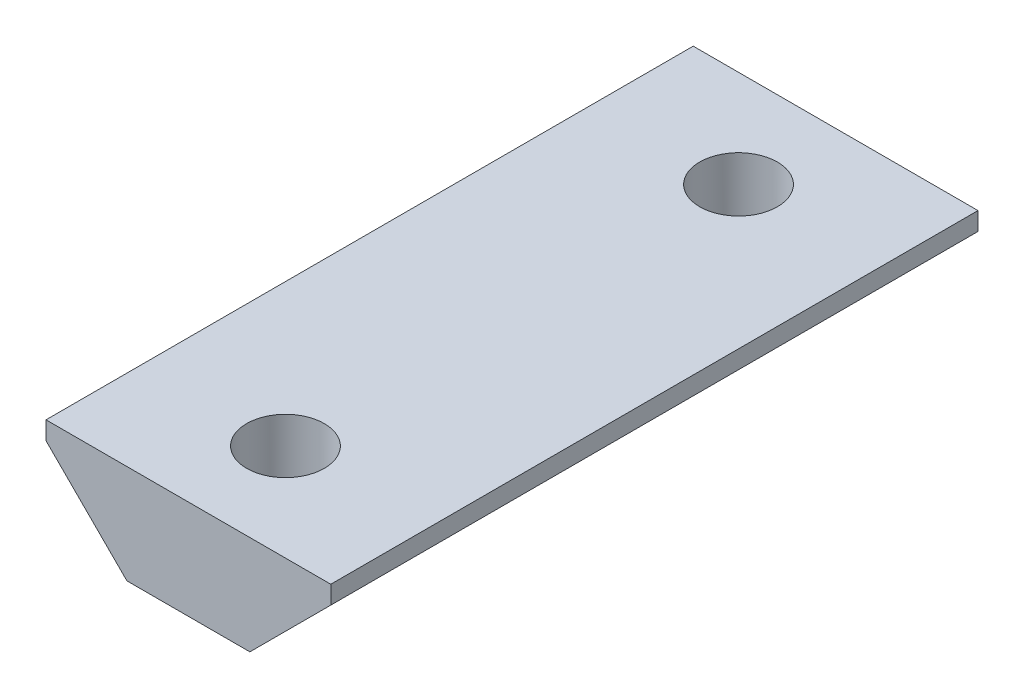
SolidWorks part; units mm, degrees
ref_plane "Ebene vorne" through (0, 0, 0) normal (0, 0, 1) x (1, 0, 0)
ref_plane "Ebene oben" through (0, 0, 0) normal (0, 1, 0) x (1, 0, 0)
ref_plane "Ebene rechts" through (0, 0, 0) normal (1, 0, 0) x (0, 0, -1)
sketch "Sketch1" plane through (0, 0, 0) normal (0, 0, 1) x (1, 0, 0)
  line L0 (0, 9.7542) -> (0, -9.4732) construction
  line L1 (4.75, 0) -> (-4.75, 0)
  line L2 (-4.75, 0) -> (-11, 6.25)
  line L3 (-11, 6.25) -> (-11, 7.65)
  line L4 (-11, 7.65) -> (11, 7.65)
  line L5 (11, 6.25) -> (11, 7.65)
  line L6 (4.75, 0) -> (11, 6.25)
  point P9 (0, 7.65)
  point P11 (0, 0)
  dimension "D1" = 1.4
  dimension "D2" = 7.65
  dimension "D3" = 11
  dimension "D4" = 135
extrude "Boss-Extrude1" add sketch "Sketch1" along normal mid plane 50
sketch "Sketch2" plane through (0, 7.65, 0) normal (0, 1, 0) x (1, 0, 0)
  circle A0 centre (0, 17.5) radius 3
  circle A1 centre (0, -17.5) radius 3
  point P4 (0, 0)
  dimension "D1" = 6
  dimension "D2" = 6
  dimension "D3" = 17.5
  dimension "D4" = 17.5
extrude "Cut-Extrude1" cut sketch "Sketch2" against normal mid plane 50
